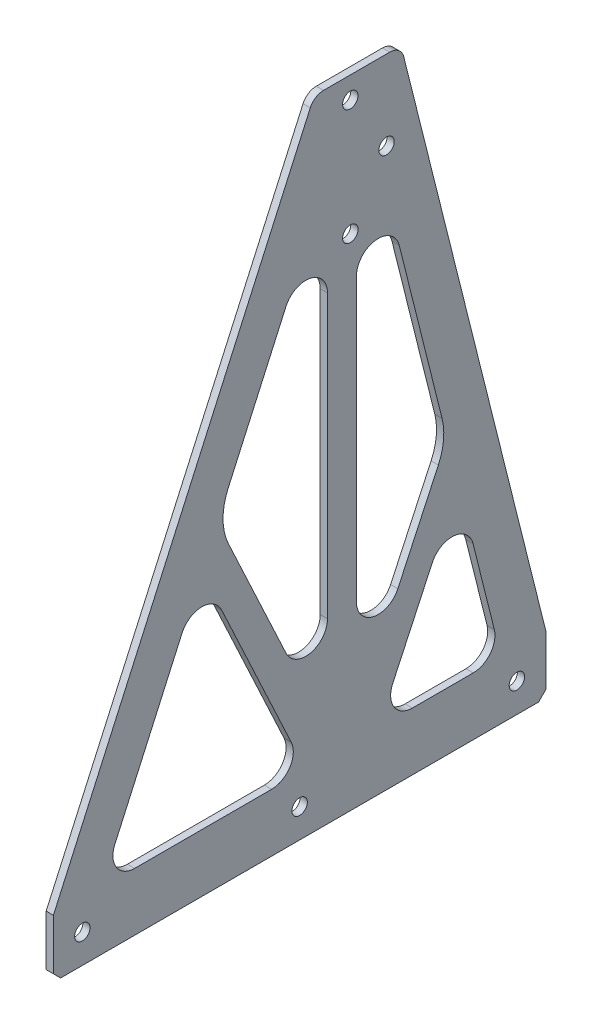
SolidWorks part; units mm, degrees
material "6061-T6 (SS)"
ref_plane "Front Plane" through (0, 0, 0) normal (0, 0, 1) x (1, 0, 0)
ref_plane "Top Plane" through (0, 0, 0) normal (0, 1, 0) x (1, 0, 0)
ref_plane "Right Plane" through (0, 0, 0) normal (1, 0, 0) x (0, 0, -1)
sketch "Sketch1" plane through (0, 0, 0) normal (1, 0, 0) x (0, 0, -1)
  line L1 (118.4058, 279.4) -> (147.4421, 279.4)
  line L2 (153.6025, 274.5901) -> (215.9, 25.4)
  line L3 (215.9, 25.4) -> (215.9, 0)
  line L4 (215.9, 0) -> (0, 0)
  line L5 (0, 25.4) -> (0, 0)
  line L6 (112.6151, 275.6558) -> (0, 25.4)
  arc A0 (112.6151, 275.6558) -> (118.4058, 279.4) centre (118.4058, 273.05) cw
  arc A1 (147.4421, 279.4) -> (153.6025, 274.5901) centre (147.4421, 273.05) cw
  point P2 (114.3, 279.4)
  point P12 (152.4, 279.4)
  dimension "D4" = 6.35
  dimension "D1" = 114.3
  dimension "D2" = 279.4
  dimension "D3" = 215.9
  dimension "D5" = 25.4
  dimension "D6" = 63.5
extrude "Boss-Extrude1" add sketch "Sketch1" along normal blind 3.175
sketch "Sketch2" [suppressed] plane through (3.175, 0, 0) normal (1, 0, 0) x (0, 0, -1)
  line L0 (-279.4, 0) -> (279.4, 0) construction
  line L1 (254, 0) -> (228.6, 0)
  line L2 (254, 0) -> (254, 19.05)
  line L3 (247.65, 25.4) -> (234.95, 25.4)
  line L4 (228.6, 0) -> (228.6, 19.05)
  line L6 (203.2, 0) -> (177.8, 0)
  line L7 (203.2, 0) -> (203.2, 19.05)
  line L8 (196.85, 25.4) -> (184.15, 25.4)
  line L9 (177.8, 0) -> (177.8, 19.05)
  line L10 (152.4, 0) -> (127, 0)
  line L11 (152.4, 0) -> (152.4, 19.05)
  line L12 (146.05, 25.4) -> (133.35, 25.4)
  line L13 (127, 0) -> (127, 19.05)
  line L14 (101.6, 0) -> (76.2, 0)
  line L15 (101.6, 0) -> (101.6, 19.05)
  line L16 (95.25, 25.4) -> (82.55, 25.4)
  line L17 (76.2, 0) -> (76.2, 19.05)
  line L18 (50.8, 0) -> (25.4, 0)
  line L19 (50.8, 0) -> (50.8, 19.05)
  line L20 (44.45, 25.4) -> (31.75, 25.4)
  line L21 (25.4, 0) -> (25.4, 19.05)
  line L22 (50.8, 0) -> (76.2, 0) construction
  line L23 (101.6, 0) -> (127, 0) construction
  line L24 (152.4, 0) -> (177.8, 0) construction
  line L25 (203.2, 0) -> (228.6, 0) construction
  line L27 (279.4, 0) -> (279.4, 12.7) construction
  line L28 (0, 609.6) -> (0, 0) construction
  arc A0 (31.75, 25.4) -> (25.4, 19.05) centre (31.75, 19.05) ccw
  arc A1 (50.8, 19.05) -> (44.45, 25.4) centre (44.45, 19.05) ccw
  arc A2 (82.55, 25.4) -> (76.2, 19.05) centre (82.55, 19.05) ccw
  arc A3 (101.6, 19.05) -> (95.25, 25.4) centre (95.25, 19.05) ccw
  arc A4 (133.35, 25.4) -> (127, 19.05) centre (133.35, 19.05) ccw
  arc A5 (152.4, 19.05) -> (146.05, 25.4) centre (146.05, 19.05) ccw
  arc A6 (184.15, 25.4) -> (177.8, 19.05) centre (184.15, 19.05) ccw
  arc A7 (203.2, 19.05) -> (196.85, 25.4) centre (196.85, 19.05) ccw
  arc A8 (234.95, 25.4) -> (228.6, 19.05) centre (234.95, 19.05) ccw
  arc A9 (254, 19.05) -> (247.65, 25.4) centre (247.65, 19.05) ccw
  point P52 (254, 25.4)
  dimension "D5" = 6.35
  dimension "D1" = 25.4
  dimension "D2" = 25.4
  dimension "D3" = 25.4
  dimension "D4" = 25.4
extrude "Cut-Extrude1" [suppressed] cut sketch "Sketch2" against normal through all
sketch "Sketch3" plane through (3.175, 0, 0) normal (1, 0, 0) x (0, 0, -1)
  line L0 (0, 0) -> (215.9, 0) construction
  line L1 (130.175, 269.875) -> (146.05, 244.475) construction
  line L2 (146.05, 244.475) -> (130.175, 219.075) construction
  line L3 (215.9, 0) -> (215.9, 25.4) construction
  circle A0 centre (146.05, 244.475) radius 3.3782
  circle A1 centre (130.175, 219.075) radius 3.3782
  circle A2 centre (130.175, 269.875) radius 3.3782
  dimension "D1" = 6.7564
  dimension "D2" = 244.475
  dimension "D3" = 69.85
  dimension "D4" = 15.875
  dimension "D6" = 50.8
extrude "Cut-Extrude2" cut sketch "Sketch3" against normal through all
sketch "Sketch4" plane through (3.175, 0, 0) normal (1, 0, 0) x (0, 0, -1)
  line L0 (0, 0) -> (215.9, 0) construction
  line L1 (0, 25.4) -> (0, 0) construction
  line L2 (215.9, 0) -> (215.9, 25.4) construction
  line L3 (12.7, 12.7) -> (203.2, 12.7) construction
  circle A0 centre (12.7, 12.7) radius 3.3782
  circle A1 centre (107.95, 12.7) radius 3.3782
  circle A2 centre (203.2, 12.7) radius 3.3782
  dimension "D1" = 12.7
  dimension "D2" = 12.7
  dimension "D3" = 12.7
  dimension "D4" = 6.7564
extrude "Cut-Extrude3" cut sketch "Sketch4" against normal through all
chamfer "Chamfer1" distance 3.175 angle 45 2 edges at (1.5875, 0, 0) (1.5875, 0, -215.9)
sketch "Sketch5" plane through (3.175, 0, 0) normal (1, 0, 0) x (0, 0, -1)
  line L0 (35.6212, 25.4) -> (95.6554, 25.4)
  line L1 (101.9521, 205.5382) -> (76.6069, 149.2154)
  line L2 (151.6288, 203.9396) -> (170.3972, 128.8662)
  line L3 (215.9, 25.4) -> (153.6025, 274.5901) construction
  line L4 (112.6151, 275.6558) -> (0, 25.4) construction
  line L5 (120.1632, 77.9211) -> (120.1632, 201.6295)
  line L6 (132.8632, 77.9211) -> (132.8632, 201.6295)
  line L7 (157.371, 25.4) -> (184.0643, 25.4)
  line L8 (3.175, 0) -> (212.725, 0) construction
  line L9 (102.0056, 73.8956) -> (76.7495, 128.0576)
  line L10 (104.2879, 38.9504) -> (73.7366, 104.4679)
  line L11 (151.0208, 73.8956) -> (168.7758, 111.9713)
  line L12 (148.7385, 38.9504) -> (166.1155, 76.2155)
  line L13 (89.3775, 100.9766) -> (77.8674, 95.6094) construction
  line L14 (159.8983, 92.9335) -> (171.4084, 87.5662) construction
  line L15 (110.6066, 25.4) -> (120.1632, 34.9566) construction
  line L16 (115.3849, 30.1783) -> (120.1632, 25.4) construction
  line L17 (183.9886, 74.5002) -> (193.3049, 37.2352)
  line L18 (56.418, 104.3512) -> (26.9351, 38.8337)
  line L19 (132.8632, 34.9566) -> (142.4198, 25.4) construction
  line L20 (137.6415, 30.1783) -> (125.4553, 17.9921) construction
  arc A0 (184.0643, 25.4) -> (193.3049, 37.2352) centre (184.0643, 34.925) ccw
  arc A1 (35.6212, 25.4) -> (26.9351, 38.8337) centre (35.6212, 34.925) cw
  arc A2 (132.8632, 201.6295) -> (151.6288, 203.9396) centre (142.3882, 201.6295) cw
  arc A3 (101.9521, 205.5382) -> (120.1632, 201.6295) centre (110.6382, 201.6295) cw
  arc A4 (166.1155, 76.2155) -> (183.9886, 74.5002) centre (174.748, 72.1901) cw
  arc A5 (73.7366, 104.4679) -> (56.418, 104.3512) centre (65.104, 100.4425) ccw
  arc A6 (104.2879, 38.9504) -> (95.6554, 25.4) centre (95.6554, 34.925) cw
  arc A7 (148.7385, 38.9504) -> (157.371, 25.4) centre (157.371, 34.925) ccw
  arc A8 (151.0208, 73.8956) -> (132.8632, 77.9211) centre (142.3882, 77.9211) cw
  arc A9 (102.0056, 73.8956) -> (120.1632, 77.9211) centre (110.6382, 77.9211) ccw
  arc A10 (168.7758, 111.9713) -> (170.3972, 128.8662) centre (145.7555, 122.7058) ccw
  arc A11 (76.7495, 128.0576) -> (76.6069, 149.2154) centre (99.7697, 138.7921) cw
  point P37 (177.4715, 100.5687)
  point P40 (64.9499, 123.3111)
  dimension "D8" = 9.525
  dimension "D9" = 9.525
  dimension "D10" = 25.4
  dimension "D1" = 25.4
  dimension "D2" = 19.05
  dimension "D3" = 19.05
  dimension "D4" = 12.7
  dimension "D5" = 12.7
  dimension "D6" = 65
  dimension "D7" = 65
extrude "Cut-Extrude4" cut sketch "Sketch5" against normal through all
